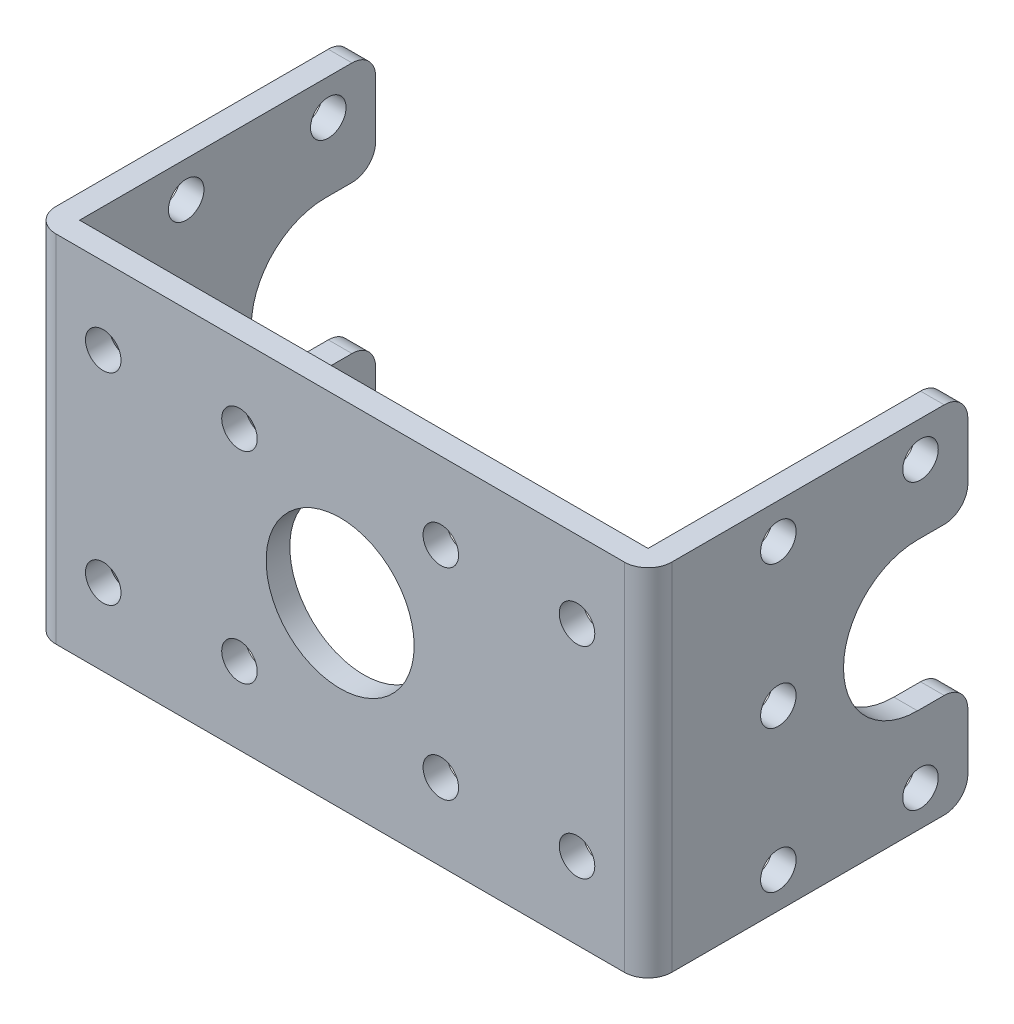
SolidWorks part; units mm, degrees
ref_plane "Front Plane" through (0, 0, 0) normal (0, 0, 1) x (1, 0, 0)
ref_plane "Top Plane" through (0, 0, 0) normal (0, 1, 0) x (1, 0, 0)
ref_plane "Right Plane" through (0, 0, 0) normal (1, 0, 0) x (0, 0, -1)
sketch "Sketch1" plane through (0, 0, 0) normal (0, 1, 0) x (1, 0, 0)
  line L0 (-24, 0) -> (24, 0) construction
  line L1 (24, 0) -> (24, -25)
  line L2 (24, -25) -> (-24, -25)
  line L3 (-24, -25) -> (-24, 0)
  line L4 (-24, 0) -> (-26, 0)
  line L5 (-26, 0) -> (-26, -27)
  line L6 (24, 0) -> (26, 0)
  line L7 (26, 0) -> (26, -27)
  line L8 (26, -27) -> (-26, -27)
  point P4 (0, 0)
  dimension "D1" = 2
  dimension "D2" = 2
  dimension "D3" = 2
  dimension "D4" = 48
  dimension "D5" = 25
extrude "Boss-Extrude1" add sketch "Sketch1" along normal blind 30
sketch "Sketch2" plane through (26, 0, 0) normal (1, 0, 0) x (0, 0, -1)
  line L0 (0, 15) -> (-10.5, 15) construction
  line L1 (0, 30) -> (0, 0) construction
  line L2 (-4, 27) -> (-4, 3) construction
  line L4 (-4.25, 21.25) -> (0, 21.25)
  line L5 (-4.25, 8.75) -> (0, 8.75)
  line L6 (0, 21.25) -> (0, 8.75)
  line L8 (-4, 27) -> (0, 27) construction
  line L11 (-10.5, 15) -> (-16, 15) construction
  arc A0 (-4.25, 21.25) -> (-4.25, 8.75) centre (-4.25, 15) ccw
  circle A1 centre (-4, 27) radius 1.5
  circle A2 centre (-4, 3) radius 1.5
  circle A3 centre (-16, 15) radius 1.5
  circle A4 centre (-16, 27) radius 1.5
  circle A5 centre (-16, 3) radius 1.5
  point P8 (-4, 15)
  dimension "D1" = 12
  dimension "D2" = 4
extrude "Cut-Extrude1" cut sketch "Sketch2" against normal through all
sketch "Sketch3" plane through (0, 0, 27) normal (0, 0, 1) x (1, 0, 0)
  line L0 (0, 0) -> (0, 30) construction
  line L1 (-26, 0) -> (26, 0) construction
  line L2 (-26, 30) -> (26, 30) construction
  line L3 (-8.5, 15) -> (8.5, 15) construction
  line L4 (8.5, 23.5) -> (8.5, 6.5) construction
  line L5 (8.5, 23.5) -> (20, 23.5) construction
  line L6 (8.5, 6.5) -> (20, 6.5) construction
  line L7 (-8.5, 23.5) -> (-8.5, 6.5) construction
  line L8 (-8.5, 6.5) -> (-20, 6.5) construction
  line L9 (-8.5, 23.5) -> (-20, 23.5) construction
  circle A0 centre (0, 15) radius 6.25
  circle A1 centre (20, 23.5) radius 1.5
  circle A2 centre (20, 6.5) radius 1.5
  circle A3 centre (8.5, 6.5) radius 1.5
  circle A4 centre (8.5, 23.5) radius 1.5
  circle A5 centre (-8.5, 6.5) radius 1.5
  circle A6 centre (-20, 6.5) radius 1.5
  circle A7 centre (-8.5, 23.5) radius 1.5
  circle A8 centre (-20, 23.5) radius 1.5
  point P11 (8.5, 15)
  dimension "D1" = 8.5
extrude "Cut-Extrude2" cut sketch "Sketch3" against normal blind 30
fillet "Fillet1" radius 2 10 edges at (-25, 21.25, 0) (-25, 30, 0) (-25, 8.75, 0) (-25, 0, 0) (25, 0, 0) (25, 8.75, 0) (25, 21.25, 0) (25, 30, 0) (26, 15, 27) (-26, 15, 27)
